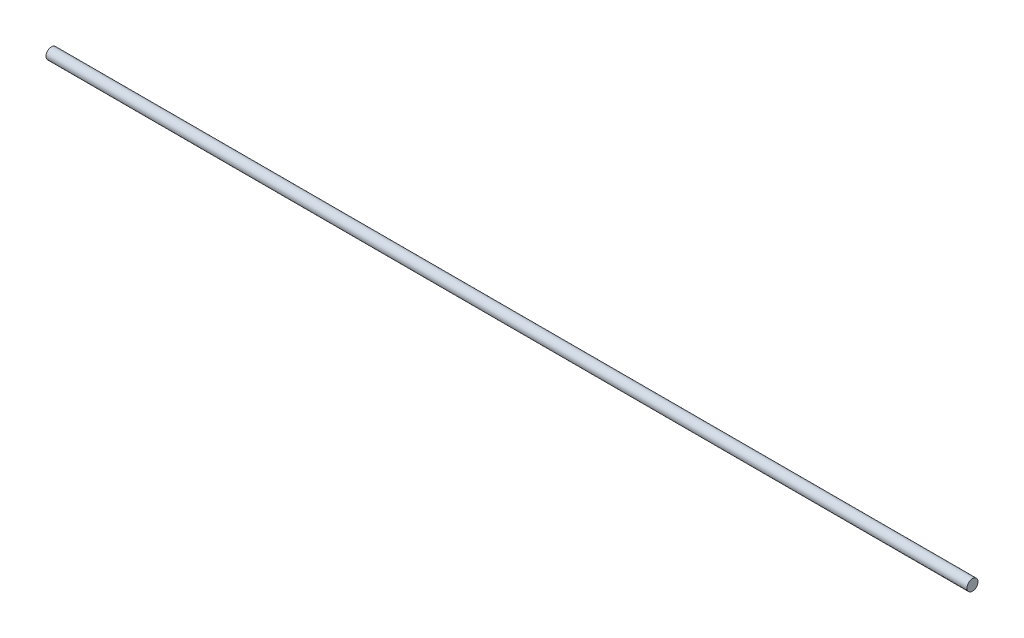
SolidWorks part; units mm, degrees
ref_plane "Front Plane" through (0, 0, 0) normal (0, 0, 1) x (1, 0, 0)
ref_plane "Top Plane" through (0, 0, 0) normal (0, 1, 0) x (1, 0, 0)
ref_plane "Right Plane" through (0, 0, 0) normal (1, 0, 0) x (0, 0, -1)
sketch "Sketch1" plane through (0, 0, 0) normal (1, 0, 0) x (0, 0, -1)
  circle A0 centre (0, 0) radius 1.651
  dimension "D1" = 3.302
extrude "Boss-Extrude1" add sketch "Sketch1" along normal blind 276.225
